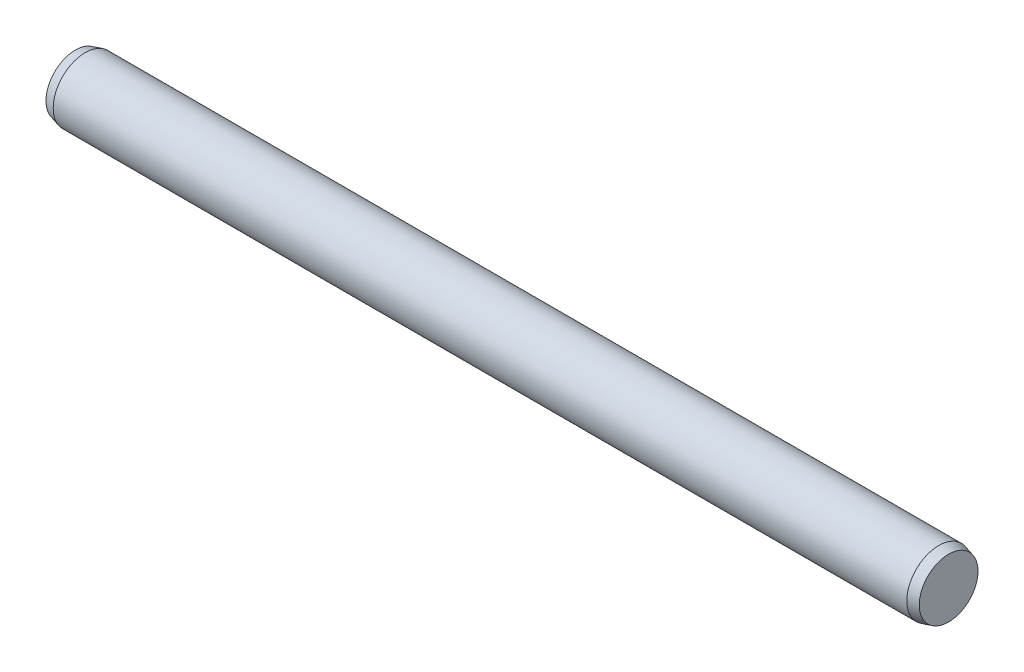
SolidWorks part; units mm, degrees
ref_plane "Front Plane" through (0, 0, 0) normal (0, 0, 1) x (1, 0, 0)
ref_plane "Top Plane" through (0, 0, 0) normal (0, 1, 0) x (1, 0, 0)
ref_plane "Right Plane" through (0, 0, 0) normal (1, 0, 0) x (0, 0, -1)
sketch "Sketch1" plane through (0, 0, 0) normal (0, 0, 1) x (1, 0, 0)
  line L0 (-10, 0) -> (10, 0) construction
  line L1 (10, 0.75) -> (10, -0.75) construction
  line L2 (-10, 0.75) -> (-10, -0.75) construction
  line L3 (10.23, 0.75) -> (10.23, -0.75) construction
  line L4 (-10.23, 0.75) -> (-10.23, -0.75) construction
  line L5 (-10, 0) -> (-10.23, 0) construction
  line L6 (10, 0) -> (10.23, 0) construction
  dimension "Dia" = 1.5
  dimension "Length" = 20
  dimension "C" = 0.23
  dimension "D1" = 0.23
sketch "Sketch2" plane through (0, 0, 0) normal (1, 0, 0) x (0, 0, -1)
  circle A0 centre (0, 0) radius 0.75
extrude "Extrude1" add sketch "Sketch2" against normal up to vertex (10 mm away) and the other way up to vertex (10 mm away) up to point (-10, 0.75, 0) other way up to point (10, 0.75, 0)
sketch "Sketch3" plane through (10, 0, 0) normal (1, 0, 0) x (0, 0, -1)
  circle A1 centre (0, 0) radius 0.75
  circle A2 centre (0, 0) radius 0.75
  dimension "D1" = 0
extrude "Extrude2" add sketch "Sketch3" along normal up to vertex (0.23 mm away) draft 15 up to point (10.23, 0, 0)
sketch "Sketch4" plane through (-10, 0, 0) normal (-1, 0, 0) x (0, 0, 1)
  circle A1 centre (0, 0) radius 0.75
  circle A2 centre (0, 0) radius 0.75
  dimension "D1" = 0
extrude "Extrude3" add sketch "Sketch4" along normal up to vertex (0.23 mm away) draft 15 up to point (-10.23, 0, 0)
equation "\"D1@Sketch1\" = \"C@Sketch1\""
